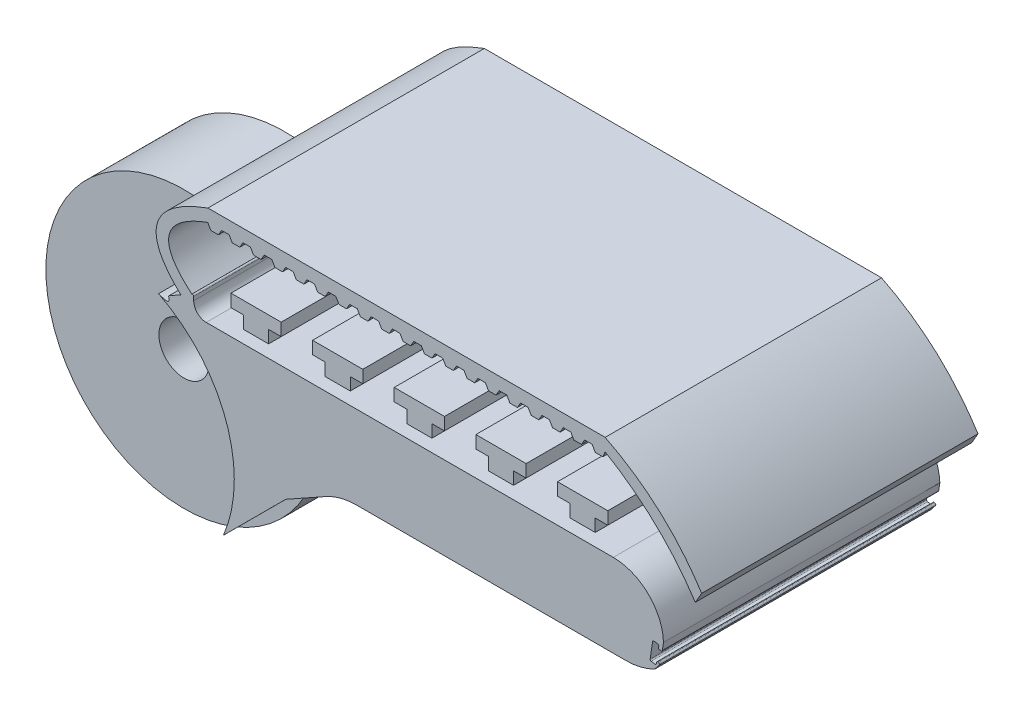
SolidWorks part; units mm, degrees
ref_plane "Front Plane" through (0, 0, 0) normal (0, 0, 1) x (1, 0, 0)
ref_plane "Top Plane" through (0, 0, 0) normal (0, 1, 0) x (1, 0, 0)
ref_plane "Right Plane" through (0, 0, 0) normal (1, 0, 0) x (0, 0, -1)
sketch "Sketch1" plane through (0, 0, 0) normal (0, 0, 1) x (1, 0, 0)
  line L0 (0, 54.6251) -> (0, -55.0389) construction
  line L3 (-16.8658, -0.5196) -> (-13.4237, -0.5196)
  line L20 (-12.4208, -7.1282) -> (-33.8605, -7.1282)
  line L21 (-36.3005, -7.7639) -> (-39.4953, -9.5501)
  line L22 (-39.4953, -9.5501) -> (-44.445, -14.4999)
  line L24 (-48.7703, -0.1487) -> (-46.973, 0.8562)
  line L26 (-9.4261, -4.3804) -> (-9.5177, -4.9729)
  line L27 (-9.6322, -5.0564) -> (-9.8294, -5.0251)
  line L28 (-46.8242, 0.7689) -> (-46.8242, 0.4804)
  line L29 (-45.8242, -0.5196) -> (-16.8658, -0.5196)
  line L30 (-9.8294, -5.0251) -> (-9.7981, -4.8283)
  line L31 (-9.8819, -4.7138) -> (-10.1776, -4.6692)
  line L32 (-10.2914, -4.7532) -> (-10.4885, -6.0612)
  line L33 (-10.4036, -6.1751) -> (-10.107, -6.217)
  line L34 (-9.994, -6.132) -> (-9.9806, -6.0372)
  line L35 (-9.8635, -5.9529) -> (-9.8322, -5.9586)
  line L36 (-9.7712, -6.1181) -> (-10.1169, -6.5657)
  arc A0 (-9.4261, -4.3804) -> (-13.4237, -0.5196) centre (-13.4237, -4.5196) ccw
  arc A16 (-44.4536, -14.51) -> (-44.445, -14.4999) centre (-50.9492, -9.0276) ccw
  arc A17 (-33.8605, -7.1282) -> (-36.3005, -7.7639) centre (-33.8605, -12.1282) ccw
  arc A18 (-12.4208, -7.1282) -> (-10.1169, -6.5657) centre (-12.4208, -2.1282) ccw
  arc A22 (-46.8242, 0.7689) -> (-46.973, 0.8562) centre (-46.9242, 0.7689) ccw
  arc A23 (-48.7703, -0.1487) -> (-48.821, -0.2261) centre (-48.7215, -0.236) ccw
  arc A24 (-46.8242, 0.4804) -> (-45.8242, -0.5196) centre (-45.8242, 0.4804) ccw
  arc A25 (-9.8322, -5.9586) -> (-9.7712, -6.1181) centre (-9.8503, -6.057) cw
  arc A26 (-9.5177, -4.9729) -> (-9.6322, -5.0564) centre (-9.6166, -4.9576) cw
  arc A27 (-9.7981, -4.8283) -> (-9.8819, -4.7138) centre (-9.8968, -4.8126) ccw
  arc A28 (-10.1776, -4.6692) -> (-10.2914, -4.7532) centre (-10.1925, -4.7681) ccw
  arc A29 (-10.4885, -6.0612) -> (-10.4036, -6.1751) centre (-10.3896, -6.0761) ccw
  arc A30 (-10.107, -6.217) -> (-9.994, -6.132) centre (-10.093, -6.118) ccw
  arc A31 (-9.9806, -6.0372) -> (-9.8635, -5.9529) centre (-9.8816, -6.0512) cw
  arc A32 (-49.6161, -0.4338) -> (-44.4536, -14.51) centre (-54.5926, -10.2438) ccw
  spline S0 degree 2 poles (-48.821, -0.2261) (-48.5625, -0.8594) (-49.6161, -0.4338) knots 0 0 0 1 1 1
  dimension "D1" = 4
  dimension "D2" = 5
  dimension "D3" = 1
  dimension "D6" = 0.1
  dimension "D7" = 0.1
  dimension "D4" = 5
  dimension "D8" = 0.1
  dimension "D9" = 22
extrude "Gripper Body" add sketch "Sketch1" along normal mid plane 22
sketch "Sketch7" plane through (0, 0, 11) normal (0, 0, 1) x (1, 0, 0)
  line L0 (-65.5926, -10.2438) -> (-54.5926, -10.2438) construction
  circle A0 centre (-54.5926, -10.2438) radius 11
  arc A1 (-49.6161, -0.4338) -> (-44.4536, -14.51) centre (-54.5926, -10.2438) ccw construction
extrude "Cut-Extrude1" cut sketch "Sketch7" against normal blind 7
sketch "Sketch8" plane through (0, 0, -11) normal (0, 0, -1) x (-1, 0, 0)
  line L0 (54.5926, -10.2438) -> (58.8972, -10.2438) construction
  circle A0 centre (54.5926, -10.2438) radius 11
extrude "Cut-Extrude2" cut sketch "Sketch8" against normal blind 7
sketch "Sketch5" plane through (0, -0.5196, 0) normal (0, 1, 0) x (1, 0, 0)
  line L0 (-13.4237, 11) -> (-45.8242, 11) construction
  line L1 (-43.8602, 10) -> (-41.8602, 10)
  line L2 (-43.8602, 10) -> (-43.8602, -10)
  line L3 (-43.8602, -10) -> (-41.8602, -10)
  line L4 (-41.8602, 10) -> (-41.8602, -10)
  dimension "D1" = 2
  dimension "D2" = 20
  dimension "D3" = 1
extrude "Silicon Holder Bottom Half" add sketch "Sketch5" along normal blind 1
sketch "Sketch6" plane through (0, 0.4804, 0) normal (0, 1, 0) x (1, 0, 0)
  line L1 (-44.8602, 10) -> (-40.8602, 10)
  line L2 (-44.8602, 10) -> (-44.8602, -10)
  line L3 (-44.8602, -10) -> (-40.8602, -10)
  line L4 (-40.8602, 10) -> (-40.8602, -10)
  line L8 (-44.8602, 0) -> (-40.8602, 0) construction
  dimension "D1" = 4
  dimension "D2" = 20
extrude "Silicon Holder Top Half" add sketch "Sketch6" along normal blind 1 contours L2 L1 L4 L3
pattern_linear "Silicon Holder Pattern" count 5 spacing 6.5 along (1, 0, 0) of "Silicon Holder Top Half", "Silicon Holder Bottom Half"
sketch "Sketch9" plane through (0, 0, 4) normal (0, 0, 1) x (1, 0, 0)
  line L0 (-54.5926, 0.7562) -> (-54.5926, -10.2438) construction
  circle A0 centre (-54.5926, -10.2438) radius 2
  arc A1 (-49.6161, -0.4338) -> (-44.4536, -14.51) centre (-54.5926, -10.2438) ccw construction
  dimension "D1" = 4
extrude "Joint Pin Hole" cut sketch "Sketch9" against normal up to next
sketch "Sketch11" plane through (-14.9726, 14.9726, 0) normal (0.7071, -0.7071, 0) x (0, 0, -1)
  line L0 (-11, -36.5389) -> (-11, -34.6804) construction
  line L1 (-11, -35.6096) -> (11, -35.6096) construction
  line L3 (11, -41.6804) -> (11, -34.6804) construction
  line L4 (0, -35.6096) -> (0, -36.2801) construction
  circle A1 centre (0, -35.6096) radius 0.7
extrude "Tendon Hole" cut sketch "Sketch11" against normal through all
sketch "Sketch12" plane through (0, -7.1282, 0) normal (0, -1, 0) x (1, 0, 0)
  line L0 (-33.8605, 0) -> (-22.8254, 0) construction
  line L1 (-33.8605, 11) -> (-33.8605, -11) construction
  line L2 (-45.8242, 0) -> (-16.8658, 0) construction
  line L4 (-25.3254, -2) -> (-20.3254, -2)
  line L5 (-25.3254, -2) -> (-25.3254, 2)
  line L6 (-25.3254, 2) -> (-20.3254, 2)
  line L7 (-20.3254, -2) -> (-20.3254, 2)
  line L8 (-25.3254, -2) -> (-20.3254, 2) construction
  line L9 (-25.3254, 2) -> (-20.3254, -2) construction
  dimension "D1" = 5
  dimension "D2" = 4
extrude "Elastic Holder" add sketch "Sketch12" along normal blind 4
sketch "Sketch14" plane through (0, -11.1282, 0) normal (0, -1, 0) x (1, 0, 0)
  line L1 (-25.3254, 2) -> (-17.3254, 2)
  line L2 (-25.3254, 2) -> (-25.3254, -2)
  line L3 (-25.3254, -2) -> (-17.3254, -2)
  line L4 (-17.3254, 2) -> (-17.3254, -2)
  dimension "D1" = 8
extrude "Boss-Extrude4" add sketch "Sketch14" along normal blind 2
fillet "Fillet8" radius 0.5 16 edges at (-25.3254, -7.1282, 0) (-22.8254, -7.1282, 2) (-22.8254, -7.1282, -2) (-25.3254, -10.1282, 2) (-20.3254, -9.1282, 2) (-18.8254, -11.1282, 2) (-17.3254, -12.1282, 2) (-20.3254, -7.1282, 0) (-18.8254, -11.1282, -2) (-17.3254, -12.1282, -2) (-17.3254, -13.1282, 0) (-21.3254, -13.1282, 2) (-25.3254, -13.1282, 0) (-21.3254, -13.1282, -2) (-25.3254, -10.1282, -2) (-20.3254, -9.1282, -2)
sketch "Sketch17" plane through (0, 0, 11) normal (0, 0, 1) x (1, 0, 0)
  line L0 (-47.8459, 0.3682) -> (-46.973, 0.8562)
  line L1 (-45.7049, 6.4339) -> (-45.4549, 6.0009)
  line L2 (-42.9049, 6.4339) -> (-42.3049, 6.4339)
  line L4 (-45.6887, 7.4338) -> (-14.0684, 7.4338)
  line L6 (-45.4549, 6.0009) -> (-44.8549, 6.0009)
  line L7 (-14.0684, 6.4339) -> (-14.0684, 7.4338)
  line L8 (-44.8549, 6.0009) -> (-44.6049, 6.4339)
  line L9 (-44.6049, 6.4339) -> (-44.0049, 6.4339)
  line L10 (-43.7549, 6.0009) -> (-44.0049, 6.4339)
  line L11 (-43.1549, 6.0009) -> (-43.7549, 6.0009)
  line L12 (-42.9049, 6.4339) -> (-43.1549, 6.0009)
  line L13 (-42.0549, 6.0009) -> (-42.3049, 6.4339)
  line L14 (-41.4549, 6.0009) -> (-42.0549, 6.0009)
  line L15 (-41.2049, 6.4339) -> (-41.4549, 6.0009)
  line L16 (-39.5049, 6.4339) -> (-38.9049, 6.4339)
  line L17 (-41.2049, 6.4339) -> (-40.6049, 6.4339)
  line L18 (-40.3549, 6.0009) -> (-40.6049, 6.4339)
  line L19 (-39.7549, 6.0009) -> (-40.3549, 6.0009)
  line L20 (-39.5049, 6.4339) -> (-39.7549, 6.0009)
  line L21 (-38.6549, 6.0009) -> (-38.9049, 6.4339)
  line L22 (-38.0549, 6.0009) -> (-38.6549, 6.0009)
  line L23 (-37.8049, 6.4339) -> (-38.0549, 6.0009)
  line L24 (-36.1049, 6.4339) -> (-35.5049, 6.4339)
  line L25 (-37.8049, 6.4339) -> (-37.2049, 6.4339)
  line L26 (-36.9549, 6.0009) -> (-37.2049, 6.4339)
  line L27 (-36.3549, 6.0009) -> (-36.9549, 6.0009)
  line L28 (-36.1049, 6.4339) -> (-36.3549, 6.0009)
  line L29 (-35.2549, 6.0009) -> (-35.5049, 6.4339)
  line L30 (-34.6549, 6.0009) -> (-35.2549, 6.0009)
  line L31 (-34.4049, 6.4339) -> (-34.6549, 6.0009)
  line L32 (-32.7049, 6.4339) -> (-32.1049, 6.4339)
  line L33 (-34.4049, 6.4339) -> (-33.8049, 6.4339)
  line L34 (-33.5549, 6.0009) -> (-33.8049, 6.4339)
  line L35 (-32.9549, 6.0009) -> (-33.5549, 6.0009)
  line L36 (-32.7049, 6.4339) -> (-32.9549, 6.0009)
  line L37 (-31.8549, 6.0009) -> (-32.1049, 6.4339)
  line L38 (-31.2549, 6.0009) -> (-31.8549, 6.0009)
  line L39 (-31.0049, 6.4339) -> (-31.2549, 6.0009)
  line L40 (-29.3049, 6.4339) -> (-28.7049, 6.4339)
  line L41 (-31.0049, 6.4339) -> (-30.4049, 6.4339)
  line L42 (-30.1549, 6.0009) -> (-30.4049, 6.4339)
  line L43 (-29.5549, 6.0009) -> (-30.1549, 6.0009)
  line L44 (-29.3049, 6.4339) -> (-29.5549, 6.0009)
  line L45 (-28.4549, 6.0009) -> (-28.7049, 6.4339)
  line L46 (-27.8549, 6.0009) -> (-28.4549, 6.0009)
  line L47 (-27.6049, 6.4339) -> (-27.8549, 6.0009)
  line L48 (-25.9049, 6.4339) -> (-25.3049, 6.4339)
  line L49 (-27.6049, 6.4339) -> (-27.0049, 6.4339)
  line L50 (-26.7549, 6.0009) -> (-27.0049, 6.4339)
  line L51 (-26.1549, 6.0009) -> (-26.7549, 6.0009)
  line L52 (-25.9049, 6.4339) -> (-26.1549, 6.0009)
  line L53 (-25.0549, 6.0009) -> (-25.3049, 6.4339)
  line L54 (-24.4549, 6.0009) -> (-25.0549, 6.0009)
  line L55 (-24.2049, 6.4339) -> (-24.4549, 6.0009)
  line L56 (-22.5049, 6.4339) -> (-21.9049, 6.4339)
  line L57 (-24.2049, 6.4339) -> (-23.6049, 6.4339)
  line L58 (-23.3549, 6.0009) -> (-23.6049, 6.4339)
  line L59 (-22.7549, 6.0009) -> (-23.3549, 6.0009)
  line L60 (-22.5049, 6.4339) -> (-22.7549, 6.0009)
  line L61 (-21.6549, 6.0009) -> (-21.9049, 6.4339)
  line L62 (-21.0549, 6.0009) -> (-21.6549, 6.0009)
  line L63 (-20.8049, 6.4339) -> (-21.0549, 6.0009)
  line L64 (-19.1049, 6.4339) -> (-18.5049, 6.4339)
  line L65 (-20.8049, 6.4339) -> (-20.2049, 6.4339)
  line L66 (-19.9549, 6.0009) -> (-20.2049, 6.4339)
  line L67 (-19.3549, 6.0009) -> (-19.9549, 6.0009)
  line L68 (-19.1049, 6.4339) -> (-19.3549, 6.0009)
  line L69 (-18.2549, 6.0009) -> (-18.5049, 6.4339)
  line L70 (-17.6549, 6.0009) -> (-18.2549, 6.0009)
  line L71 (-17.4049, 6.4339) -> (-17.6549, 6.0009)
  line L72 (-15.7049, 6.4339) -> (-15.1049, 6.4339)
  line L73 (-17.4049, 6.4339) -> (-16.8049, 6.4339)
  line L74 (-16.5549, 6.0009) -> (-16.8049, 6.4339)
  line L75 (-15.9549, 6.0009) -> (-16.5549, 6.0009)
  line L76 (-15.7049, 6.4339) -> (-15.9549, 6.0009)
  line L77 (-14.8549, 6.0009) -> (-15.1049, 6.4339)
  line L78 (-14.2549, 6.0009) -> (-14.8549, 6.0009)
  line L79 (-14.0684, 6.4339) -> (-14.2549, 6.0009)
  spline S0 degree 2 poles (-46.973, 0.8562) (-51.2197, 4.4278) (-45.7049, 6.4339) knots 0 0 0 1 1 1
  spline S1 degree 2 poles (-47.8459, 0.3682) (-52.665, 4.8978) (-45.6887, 7.4338) knots 0 0 0 1 1 1
  dimension "D1" = 1
  dimension "D2" = 1
extrude "Mould" add sketch "Sketch17" against normal blind 22
sketch "Sketch18" plane through (0, 0, -11) normal (0, 0, -1) x (-1, 0, 0)
  line L5 (14.0684, 6.4339) -> (14.0684, 7.4338) construction
  point P2 (0, 0)
  point P6 (0, 0)
  point P7 (0, 0)
  point P10 (0, 0)
  point P11 (0, 0)
  line B0 (14.0684, 7.4338) -> (14.0684, 6.4339)
  line B1 (6.8899, -0.3486) -> (6.3899, 0.5174)
  spline B2 degree 2 poles (14.0684, 6.4339) (9.6936, 3.8655) (6.8899, -0.3486) knots 0 0 0 1 1 1
  spline B3 degree 2 poles (6.3899, 0.5174) (9.2631, 5.0144) (14.0684, 7.4338) knots 0 0 0 1 1 1
sketch_block_instance "Block1-1"
sketch_block "Block1"
extrude "Extra Mould Area onto Fingernail" add sketch "Sketch18" against normal blind 22
